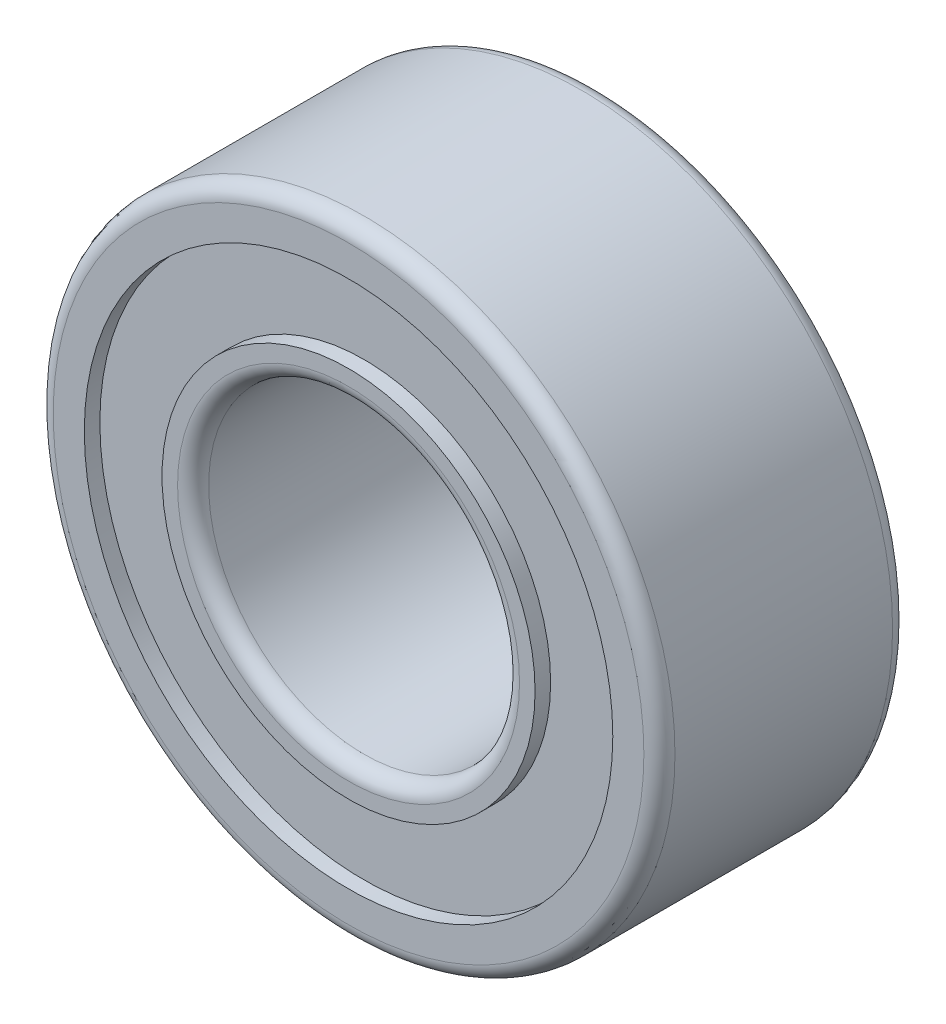
SolidWorks part; units mm, degrees
ref_plane "Front Plane" through (0, 0, 0) normal (0, 0, 1) x (1, 0, 0)
ref_plane "Top Plane" through (0, 0, 0) normal (0, 1, 0) x (1, 0, 0)
ref_plane "Right Plane" through (0, 0, 0) normal (1, 0, 0) x (0, 0, -1)
sketch "Sketch1" plane through (0, 0, 0) normal (0, 0, 1) x (1, 0, 0)
  circle A0 centre (0, 0) radius 5
  circle A1 centre (0, 0) radius 2.5
  dimension "D1" = 10
  dimension "D2" = 5
extrude "Boss-Extrude1" add sketch "Sketch1" along normal blind 4
fillet "Fillet1" radius 0.25 2 edges at (5, 0, 0) (5, 0, 4)
fillet "Fillet2" radius 0.25 2 edges at (2.5, 0, 0) (2.5, 0, 4)
sketch "Sketch2" plane through (0, 0, 4) normal (0, 0, 1) x (1, 0, 0)
  circle A0 centre (0, 0) radius 3
  circle A1 centre (0, 0) radius 4.25
  dimension "D1" = 6
  dimension "D2" = 8.5
extrude "Cut-Extrude1" cut sketch "Sketch2" against normal blind 0.25
sketch "Sketch3" plane through (0, 0, 0) normal (0, 0, -1) x (-1, 0, 0)
  circle A0 centre (0, 0) radius 3
  circle A1 centre (0, 0) radius 4.25
  dimension "D1" = 6
  dimension "D2" = 8.5
extrude "Cut-Extrude2" cut sketch "Sketch3" against normal blind 0.25
